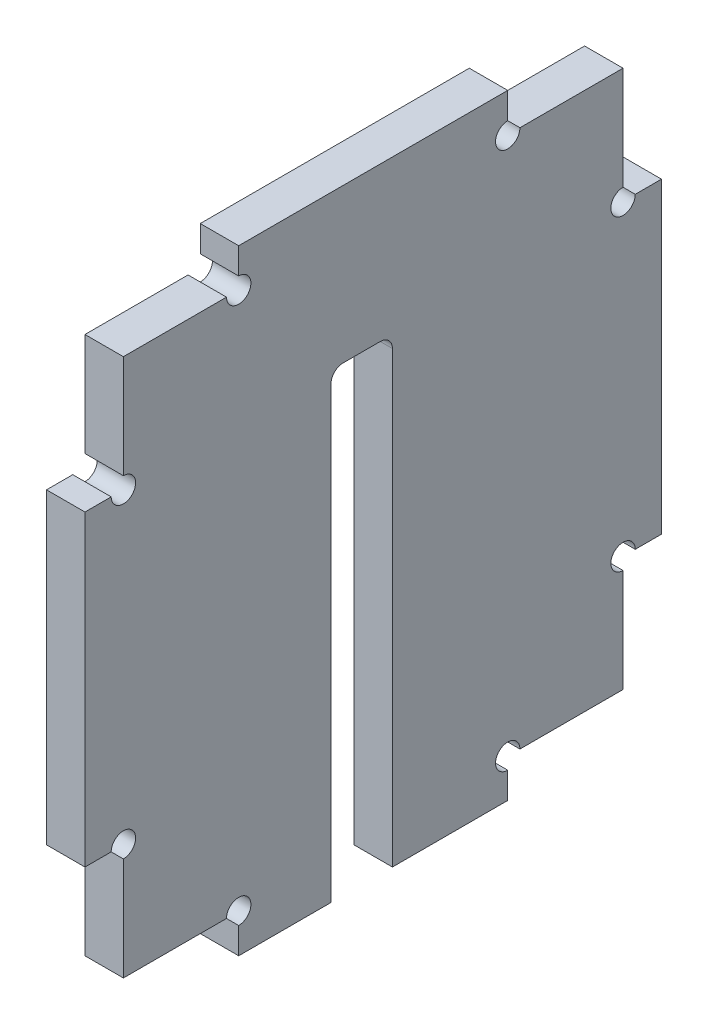
SolidWorks part; units mm, degrees
material "Acrylic (Medium-high impact)"
ref_plane "Front Plane" through (0, 0, 0) normal (0, 0, 1) x (1, 0, 0)
ref_plane "Top Plane" through (0, 0, 0) normal (0, 1, 0) x (1, 0, 0)
ref_plane "Right Plane" through (0, 0, 0) normal (1, 0, 0) x (0, 0, -1)
sketch "Sketch1" plane through (0, 0, 0) normal (1, 0, 0) x (0, 0, -1)
  line L1 (-37.5, -40) -> (37.5, -40)
  line L2 (-37.5, -40) -> (-37.5, 40)
  line L3 (-37.5, 40) -> (37.5, 40)
  line L4 (37.5, -40) -> (37.5, 40)
  line L5 (-37.5, -40) -> (37.5, 40) construction
  line L6 (-37.5, 40) -> (37.5, -40) construction
  point P0 (0, 0)
  dimension "D1" = 75
  dimension "D2" = 80
extrude "Boss-Extrude1" add sketch "Sketch1" along normal blind 5
sketch "Sketch3" plane through (5, 0, 0) normal (1, 0, 0) x (0, 0, -1)
  line L0 (-37.5, 20) -> (-32.5, 20)
  line L1 (-37.5, 40) -> (-37.5, -40) construction
  line L2 (-32.5, 20) -> (-32.5, 35)
  line L3 (-32.5, 35) -> (-17.5, 35)
  line L4 (-17.5, 35) -> (-17.5, 40)
  line L5 (37.5, 40) -> (-37.5, 40) construction
  line L6 (-17.5, 40) -> (-37.5, 40)
  line L7 (-37.5, 40) -> (-37.5, 20)
  dimension "D1" = 20
  dimension "D2" = 5
extrude "Cut-Extrude1" cut sketch "Sketch3" against normal through all both and the other way through all
mirror "Mirror1" about plane through (0, 0, 0) normal (0, 0, 1) of "Cut-Extrude1" second plane through (0, 0, 0) second plane normal (0, 1, 0)
sketch "Sketch4" plane through (5, 0, 0) normal (1, 0, 0) x (0, 0, -1)
  line L0 (37.5, -20) -> (37.5, 20) construction
  line L2 (-5.5, -40) -> (-5.5, 18.4125)
  line L3 (-3.9125, 20) -> (0.9125, 20)
  line L4 (2.5, -40) -> (2.5, 18.4125)
  line L7 (17.5, 40) -> (-17.5, 40) construction
  line L8 (-17.5, -40) -> (17.5, -40) construction
  line L9 (2.5, -40) -> (-5.5, -40)
  arc A0 (0.9125, 20) -> (2.5, 18.4125) centre (0.9125, 18.4125) cw
  arc A1 (-3.9125, 20) -> (-5.5, 18.4125) centre (-3.9125, 18.4125) ccw
  point P12 (2.5, 20)
  point P15 (-5.5, 20)
  dimension "D2" = 1.5875
  dimension "D1" = 8
  dimension "D3" = 35
  dimension "D4" = 20
extrude "Cut-Extrude2" cut sketch "Sketch4" against normal through all both
sketch "Sketch5" plane through (5, 0, 0) normal (1, 0, 0) x (0, 0, -1)
  circle A0 centre (-17.5, 35) radius 1.5875
  circle A1 centre (-32.5, 20) radius 1.5875
  circle A2 centre (17.5, 35) radius 1.5875
  circle A3 centre (32.5, 20) radius 1.5875
  circle A4 centre (32.5, -20) radius 1.5875
  circle A5 centre (17.5, -35) radius 1.5875
  circle A6 centre (-17.5, -35) radius 1.5875
  circle A7 centre (-32.5, -20) radius 1.5875
  dimension "D1" = 3.175
extrude "Cut-Extrude3" cut sketch "Sketch5" against normal through all
equation "\"cortador\"=3.175"
equation "\"D1@Sketch5\"=\"cortador\""
equation "\"D2@Sketch4\"=\"cortador\"/2"
